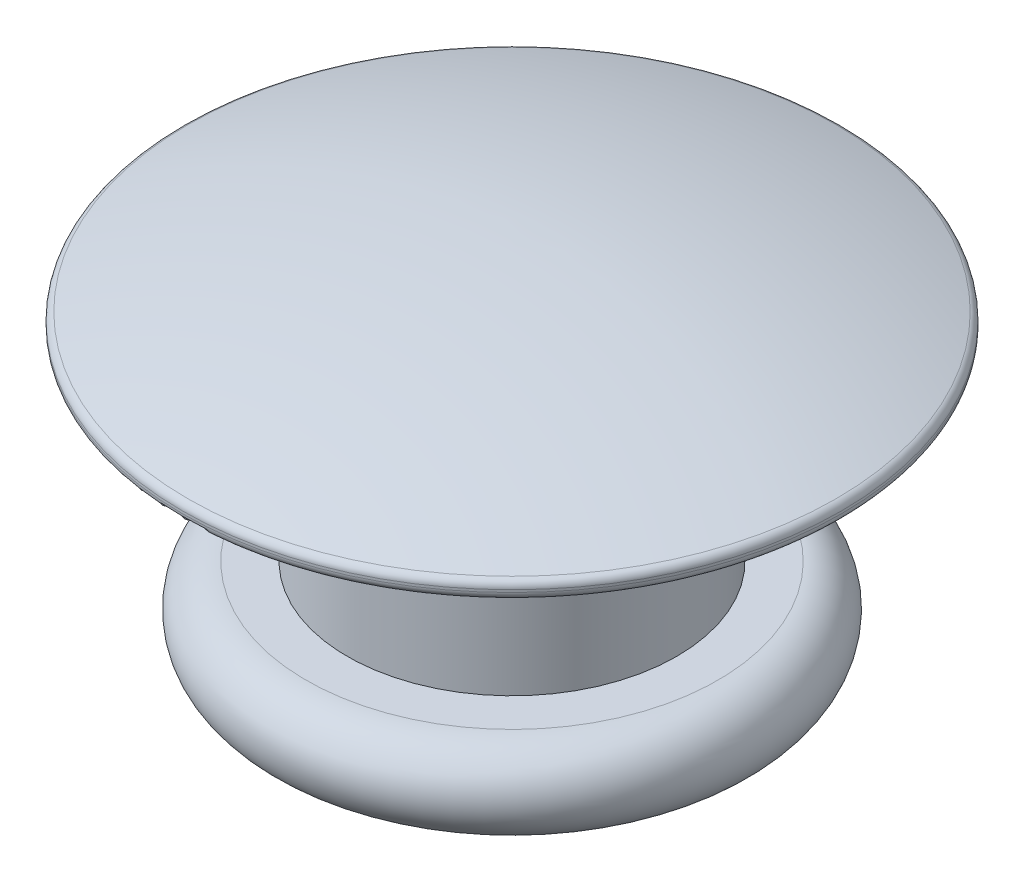
SolidWorks part; units mm, degrees
ref_plane "Front" through (0, 0, 0) normal (0, 0, 1) x (1, 0, 0)
ref_plane "Top" through (0, 0, 0) normal (0, 1, 0) x (1, 0, 0)
ref_plane "Right" through (0, 0, 0) normal (1, 0, 0) x (0, 0, -1)
sketch "Sketch1" plane through (0, 0, 0) normal (0, 0, 1) x (1, 0, 0)
  line L0 (0, 0) -> (0, 0.9) construction
  line L1 (0, 0.9) -> (-41.4186, 0.9) construction
  line L2 (4, 0.1296) -> (4, 0.1)
  line L3 (3.9, 0) -> (2, 0)
  line L4 (2, 0) -> (2, -2.4)
  line L5 (2, -2.4) -> (2.5, -2.4)
  line L6 (2.5, -3.4) -> (1.9, -3.4)
  line L7 (1.4, -2.9) -> (0, -2.9)
  line L8 (0, 0) -> (0, -2.9) construction
  line L9 (0, 0.9) -> (0, -2.9)
  arc A0 (0, 0.9) -> (3.9334, 0.2238) centre (0, -10.8786) cw
  arc A1 (2.5, -2.4) -> (2.5, -3.4) centre (2.5, -2.9) cw
  arc A2 (1.9, -3.4) -> (1.4, -2.9) centre (1.9, -2.9) cw
  arc A3 (3.9334, 0.2238) -> (4, 0.1296) centre (3.9, 0.1296) cw
  arc A4 (4, 0.1) -> (3.9, 0) centre (3.9, 0.1) cw
  point P18 (4, 0.2)
  point P21 (4, 0)
  dimension "D6" = 0.1
  dimension "D10" = 0.5
  dimension "D1" = 4
  dimension "D2" = 2.4
  dimension "D3" = 8
  dimension "D4" = 0.9
  dimension "D5" = 0.2
  dimension "D7" = 2.8
  dimension "D8" = 1
  dimension "D9" = 6
revolve "Revolve1" add sketch "Sketch1" angle 360 about L8
